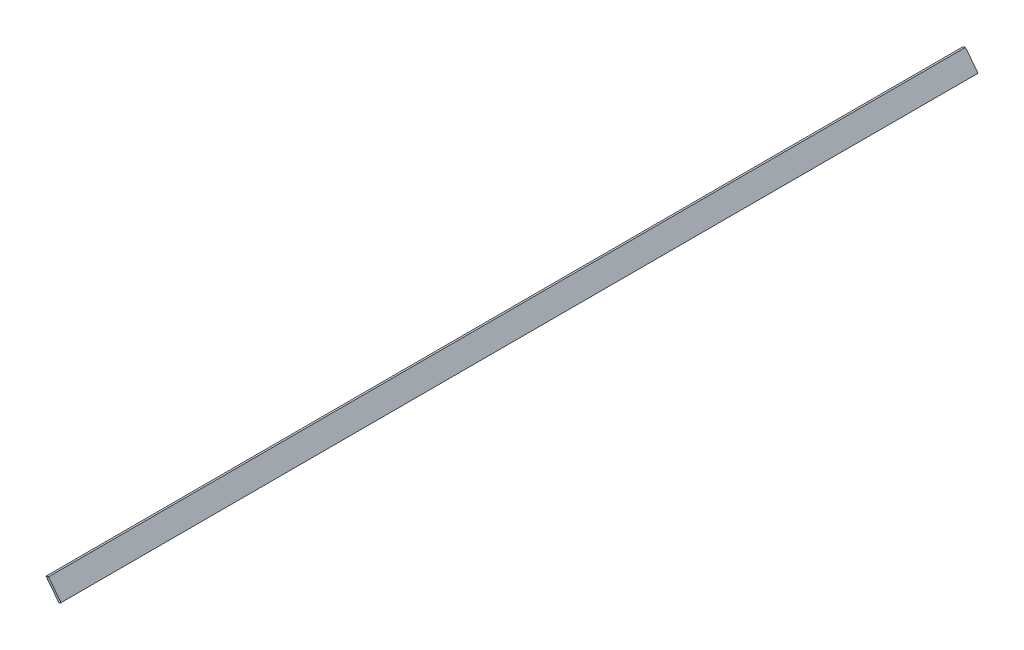
SolidWorks part; units mm, degrees
ref_plane "Front Plane" through (0, 0, 0) normal (0, 0, 1) x (1, 0, 0)
ref_plane "Top Plane" through (0, 0, 0) normal (0, 1, 0) x (1, 0, 0)
ref_plane "Right Plane" through (0, 0, 0) normal (1, 0, 0) x (0, 0, -1)
sketch "Sketch1" plane through (0, 0, 0) normal (0, 0, 1) x (1, 0, 0)
  line L0 (0, 0) -> (1.8691, 1.4444)
  line L1 (1.8691, 1.4444) -> (-10.4237, 17.3516)
  line L2 (-10.4237, 17.3516) -> (-12.8911, 16.6814)
  line L3 (-12.8911, 16.6814) -> (0, 0)
  dimension "D1" = 2.3622
  dimension "D2" = 67.5
  dimension "D3" = 90
  dimension "D4" = 21.082
extrude "Boss-Extrude1" add sketch "Sketch1" along normal blind 901.7
